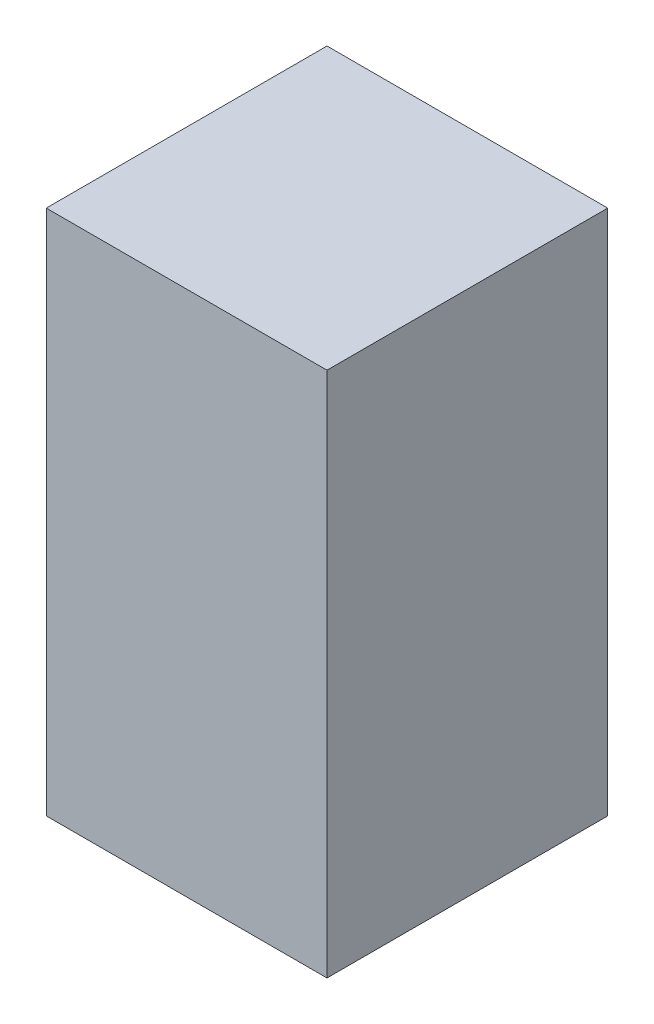
SolidWorks part; units mm, degrees
ref_plane "Plan de face" through (0, 0, 0) normal (0, 0, 1) x (1, 0, 0)
ref_plane "Plan de dessus" through (0, 0, 0) normal (0, 1, 0) x (1, 0, 0)
ref_plane "Plan de droite" through (0, 0, 0) normal (1, 0, 0) x (0, 0, -1)
sketch "Esquisse1" plane through (0, 0, 0) normal (0, 0, 1) x (1, 0, 0)
  line L0 (-1.3836, 0) -> (1.5164, 0) construction
  line L1 (0, 1.23) -> (0, -1.03) construction
  line L3 (-0.4, 0.75) -> (0.4, 0.75)
  line L4 (-0.4, 0.75) -> (-0.4, -0.75)
  line L5 (-0.4, -0.75) -> (0.4, -0.75)
  line L6 (0.4, 0.75) -> (0.4, -0.75)
  dimension "D1" = 1.5
  dimension "D2" = 0.8
extrude "Boss.-Extru.1" add sketch "Esquisse1" along normal blind 0.8
